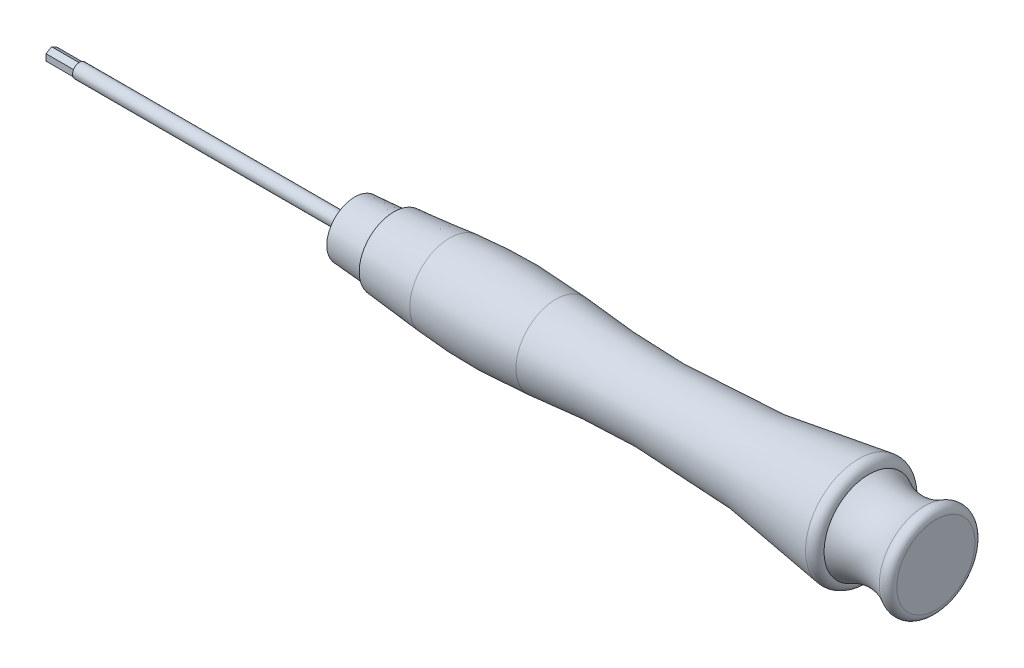
SolidWorks part; units mm, degrees
ref_plane "Front Plane" through (0, 0, 0) normal (0, 0, 1) x (1, 0, 0)
ref_plane "Top Plane" through (0, 0, 0) normal (0, 1, 0) x (1, 0, 0)
ref_plane "Right Plane" through (0, 0, 0) normal (1, 0, 0) x (0, 0, -1)
ref_axis "Axis1" through (184.722, 0, 0) along (-1, 0, 0)
sketch "Sketch1" plane through (0, 0, 0) normal (0, 0, 1) x (1, 0, 0)
  line L0 (184.722, 0) -> (-61.3483, 0) construction
  line L2 (5, 1.25) -> (59.5, 1.25)
  line L3 (59.5, 1.25) -> (59.5, 0)
  line L5 (5, 0) -> (59.5, 0)
  line L7 (5, 1.25) -> (5, 0)
  point P1 (4.5231, 0)
  point P6 (5, 2.2384)
  point P7 (35.5, 1.25)
  point P8 (0, 0)
  point P9 (0, 0)
  point P10 (5.4667, 1.25)
  point P11 (5, 1.25)
  point P12 (4.8902, 1.25)
  dimension "D1" = 5
  dimension "D3" = 1.25
  dimension "D8" = 54.5
revolve "AluminiumPart" add sketch "Sketch1" angle 360 about axis through (184.722, 0, 0) along (-1, 0, 0)
sketch "Sketch2" plane through (5, 0, 0) normal (-1, 0, 0) x (0, 0, 1)
  line L0 (-2.8, 1.6166) -> (0, 3.2332)
  line L1 (0, 3.2332) -> (2.8, 1.6166)
  line L2 (2.8, 1.6166) -> (2.8, -1.6166)
  line L3 (2.8, -1.6166) -> (0, -3.2332)
  line L4 (0, -3.2332) -> (-2.8, -1.6166)
  line L5 (-2.8, -1.6166) -> (-2.8, 1.6166)
  circle A0 centre (0, 0) radius 3.2332 construction
  dimension "D1" = 5.6
extrude "HexagonalHead" cut sketch "Sketch2" against normal blind 5.25
sketch "Sketch4" plane through (0, 0, 0) normal (0, 0, 1) x (1, 0, 0)
  line L0 (59.5, 0) -> (59.5, 5)
  line L2 (59.5, 5) -> (66.5, 5.5)
  line L3 (66.5, 5.5) -> (66.5, 0)
  line L4 (66.5, 0) -> (59.5, 0)
  line L6 (59.5, -1.25) -> (59.5, 1.25) construction
  line L7 (184.722, 0) -> (-61.3483, 0) construction
  point P2 (60.5, 0.3134)
  point P3 (0, 0)
  point P4 (0, 0)
  point P7 (60.5, 0)
  point P8 (60.5, 0)
  point P9 (0, 0)
  point P10 (59.5, 0)
  point P14 (66.5, 0)
  dimension "D1" = 7
  dimension "D2" = 5.5
  dimension "D3" = 5
revolve "FirstGreenPart" add sketch "Sketch4" angle 360 about axis through (184.722, 0, 0) along (-1, 0, 0)
sketch "Sketch5" plane through (0, 0, 0) normal (0, 0, 1) x (1, 0, 0)
  line L0 (66.5, 6.1957) -> (76.5, 7.15)
  line L1 (66.5, -5.5) -> (66.5, 5.5) construction
  line L2 (95.5, 7.15) -> (95.5, 0)
  line L3 (184.722, 0) -> (-61.3483, 0) construction
  line L4 (95.5, 0) -> (66.5, 0)
  line L5 (66.5, 0) -> (66.5, 6.1957)
  arc A0 (95.5, 7.15) -> (76.5, 7.15) centre (86, -92.3977) ccw
  point P13 (86, 7.6023)
  dimension "D2" = 7.15
  dimension "D1" = 29
  dimension "D3" = 10
  dimension "D4" = 100
revolve "FirstBlackPart" add sketch "Sketch5" angle 360 about axis through (184.722, 0, 0) along (-1, 0, 0)
sketch "Sketch6" plane through (0, 0, 0) normal (0, 0, 1) x (1, 0, 0)
  line L0 (151.5, 8) -> (151.5, 0)
  line L1 (151.5, 0) -> (95.5, 0)
  line L2 (184.722, 0) -> (-61.3483, 0) construction
  line L3 (95.5, 0) -> (95.5, 7.15)
  line L4 (95.5, -7.15) -> (95.5, 7.15) construction
  arc A0 (149.6699, 9.5) -> (95.5, 7.15) centre (115.029, 182.4976) cw
  arc A1 (149.6699, 9.5) -> (151.5, 8) centre (149.9702, 8) cw
  arc A4 (95.5, 7.15) -> (76.5, 7.15) centre (86, -92.3977) ccw construction
  point P1 (118.5, 6.1)
  point P15 (95.5, 7.15)
  dimension "D5" = 23
  dimension "D1" = 56
  dimension "D2" = 8
  dimension "D3" = 9.5
  dimension "D4" = 6.1
revolve "SecondGreenPart" add sketch "Sketch6" angle 360 about axis through (184.722, 0, 0) along (-1, 0, 0)
sketch "Sketch7" plane through (0, 0, 0) normal (0, 0, 1) x (1, 0, 0)
  line L0 (151.5, 0) -> (151.5, 8)
  line L1 (151.5, 0) -> (163.5, 0)
  line L2 (163.5, 0) -> (163.5, 7)
  line L3 (184.722, 0) -> (-61.3483, 0) construction
  arc A0 (161.5, 8.1267) -> (151.5, 8) centre (156.3924, 16.5561) cw
  arc A1 (161.5, 8.1267) -> (163.5, 7) centre (162.1827, 7) cw
  point P17 (156.3924, 6.7)
  dimension "D1" = 12
  dimension "D2" = 7
  dimension "D3" = 2
  dimension "D4" = 6.7
revolve "LastBlackPart" add sketch "Sketch7" angle 360 about axis through (184.722, 0, 0) along (-1, 0, 0)
sketch "Sketch8" plane through (10.25, 0, 0) normal (-1, 0, 0) x (0, 0, 1)
  line L0 (-1, 0.5774) -> (0, 1.1547)
  line L1 (0, 1.1547) -> (1, 0.5774)
  line L2 (1, 0.5774) -> (1, -0.5774)
  line L3 (1, -0.5774) -> (0, -1.1547)
  line L4 (0, -1.1547) -> (-1, -0.5774)
  line L5 (-1, -0.5774) -> (-1, 0.5774)
  circle A0 centre (0, 0) radius 1.1547 construction
  point P7 (-0.4344, -0.9761)
  point P10 (-1.0309, -0.2485)
  point P11 (-0.7348, 0.7646)
  point P12 (0.4577, 0.9566)
  point P13 (1.0181, 0.0319)
  point P14 (0.7679, -0.8221)
  dimension "D1" = 2
extrude "Boss-Extrude1" add sketch "Sketch8" along normal blind 5
